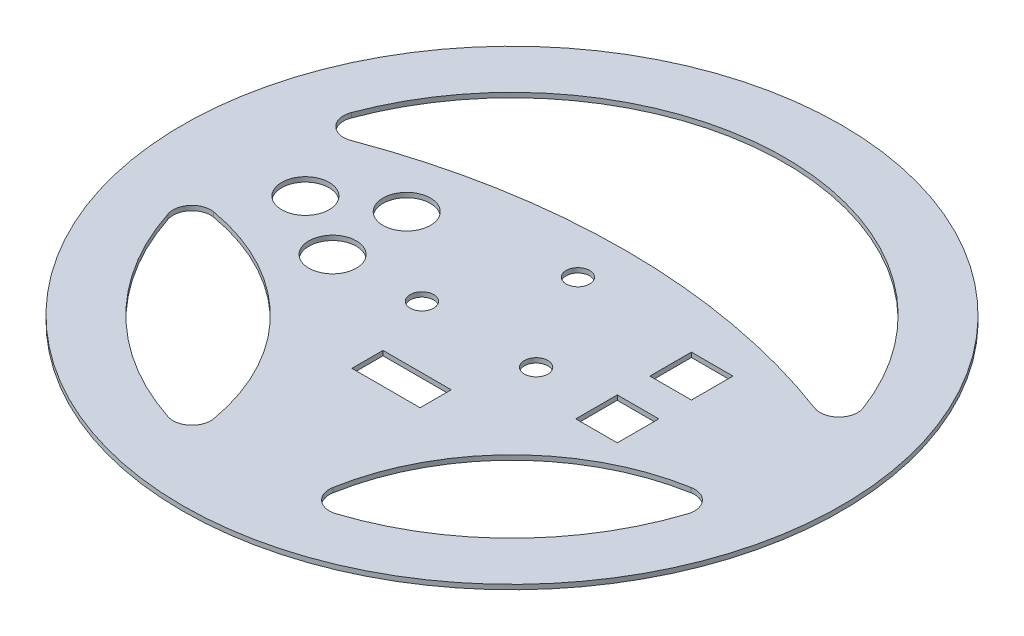
SolidWorks part; units mm, degrees
material "Thornel Mat VMA"
ref_plane "Front Plane" through (0, 0, 0) normal (0, 0, 1) x (1, 0, 0)
ref_plane "Top Plane" through (0, 0, 0) normal (0, 1, 0) x (1, 0, 0)
ref_plane "Right Plane" through (0, 0, 0) normal (1, 0, 0) x (0, 0, -1)
sketch "Sketch1" plane through (0, 0, 0) normal (0, 1, 0) x (1, 0, 0)
  line L0 (-145.7006, 0) -> (145.7006, 0) construction
  line L1 (0, -25.4) -> (0, 25.4) construction
  line L4 (0, 25.4) -> (0, 167.2109) construction
  line L5 (90.0828, -19.05) -> (90.0828, 19.05) construction
  line L7 (-90.0828, -19.05) -> (-90.0828, 19.05) construction
  line L9 (0, -25.4) -> (0, -146.1637) construction
  line L11 (-19.05, -90.0828) -> (19.05, -90.0828) construction
  line L27 (48, -12.5) -> (48, 12.5) construction
  line L28 (41, 19.5) -> (41, 5.5)
  line L29 (-11.5, -42.4964) -> (11.5, -42.4964)
  line L30 (-11.5, -42.4964) -> (-11.5, -31.9964)
  line L31 (11.5, -42.4964) -> (11.5, -31.9964)
  line L32 (-11.5, -31.9964) -> (11.5, -31.9964)
  line L33 (-11.5, -42.4964) -> (11.5, -31.9964) construction
  line L34 (11.5, -42.4964) -> (-11.5, -31.9964) construction
  line L40 (-64.6828, -43.177) -> (-64.6828, 43.177) construction
  line L42 (-21.7909, -73.025) -> (21.7909, -73.025) construction
  line L44 (41, 19.5) -> (55, 19.5)
  line L45 (41, 5.5) -> (55, 5.5)
  line L46 (55, 19.5) -> (55, 5.5)
  line L47 (41, 19.5) -> (55, 5.5) construction
  line L48 (41, 5.5) -> (55, 19.5) construction
  line L49 (41, -19.5) -> (41, -5.5)
  line L50 (41, -19.5) -> (55, -19.5)
  line L51 (41, -5.5) -> (55, -5.5)
  line L52 (55, -19.5) -> (55, -5.5)
  line L53 (41, -19.5) -> (55, -5.5) construction
  line L54 (41, -5.5) -> (55, -19.5) construction
  circle A0 centre (0, 0) radius 22.225 construction
  circle A1 centre (0, 22.225) radius 3.9688
  circle A2 centre (19.2474, -11.1125) radius 3.9688
  circle A3 centre (-19.2474, -11.1125) radius 3.9688
  circle A4 centre (0, 0) radius 111.125
  arc A7 (86.2998, 32.0959) -> (-86.2998, 32.0959) centre (0, 0) ccw
  arc A8 (-80.4848, -20.0886) -> (-20.0886, -80.4848) centre (-93.2577, -93.2577) cw
  arc A9 (20.0886, -80.4848) -> (80.4848, -20.0886) centre (93.2577, -93.2577) cw
  arc A10 (78.1188, 23.9365) -> (-78.1188, 23.9365) centre (0, -184.4146) ccw
  arc A11 (-87.6195, -28.2954) -> (-28.2954, -87.6195) centre (0, 0) ccw
  arc A12 (28.2954, -87.6195) -> (87.6195, -28.2954) centre (0, 0) ccw
  arc A13 (86.2998, 32.0959) -> (78.1188, 23.9365) centre (80.3481, 29.8824) cw
  arc A14 (-78.1188, 23.9365) -> (-86.2998, 32.0959) centre (-80.3481, 29.8824) cw
  arc A15 (-80.4848, -20.0886) -> (-87.6195, -28.2954) centre (-81.5768, -26.344) ccw
  arc A16 (87.6195, -28.2954) -> (80.4848, -20.0886) centre (81.5768, -26.344) ccw
  arc A17 (28.2954, -87.6195) -> (20.0886, -80.4848) centre (26.344, -81.5768) cw
  arc A18 (-28.2954, -87.6195) -> (-20.0886, -80.4848) centre (-26.344, -81.5768) ccw
  circle A22 centre (-48, -12.5) radius 8
  circle A23 centre (-69.6506, 0) radius 8
  circle A24 centre (-48, 12.5) radius 8
  circle A25 centre (0, 0) radius 101.6 construction
  point P11 (0, 0)
  point P15 (0, 0)
  point P18 (0, 0)
  point P21 (0, 25.4)
  point P22 (90.0828, 0)
  point P24 (0, -25.4)
  point P26 (-90.0828, 0)
  point P31 (0, -90.0828)
  point P32 (0, 38.1)
  point P63 (-64.6828, -24.6987)
  point P64 (48, 0)
  point P70 (65, 0)
  point P71 (0, -37.2464)
  point P73 (-64.6828, 0)
  point P78 (-64.6828, 28.4912)
  point P79 (-64.6828, -24.6987)
  point P80 (-64.6828, 28.4912)
  point P81 (0, -111.125)
  point P84 (0, -86.8816)
  point P89 (0, -73.025)
  dimension "D1" = 44.45
  dimension "D2" = 7.9375
  dimension "D4" = 222.25
  dimension "D5" = 19.05
  dimension "D6" = 38.1
  dimension "D10" = 74.2756
  dimension "D11" = 74.2756
  dimension "D12" = 6.35
  dimension "D14" = 14
  dimension "D15" = 14
  dimension "D19" = 25.4
  dimension "D7" = 38.1
  dimension "D8" = 38.1
  dimension "D9" = 38.1
  dimension "D13" = 25
  dimension "D16" = 14
  dimension "D18" = 48
  dimension "D20" = 38.1
  dimension "D21" = 10.5
  dimension "D22" = 23
  dimension "D23" = 65
  dimension "D24" = 43.5818
  dimension "14" = 14
  dimension "D3" = 3
extrude "Boss-Extrude1" add sketch "Sketch1" along normal blind 1.5875
